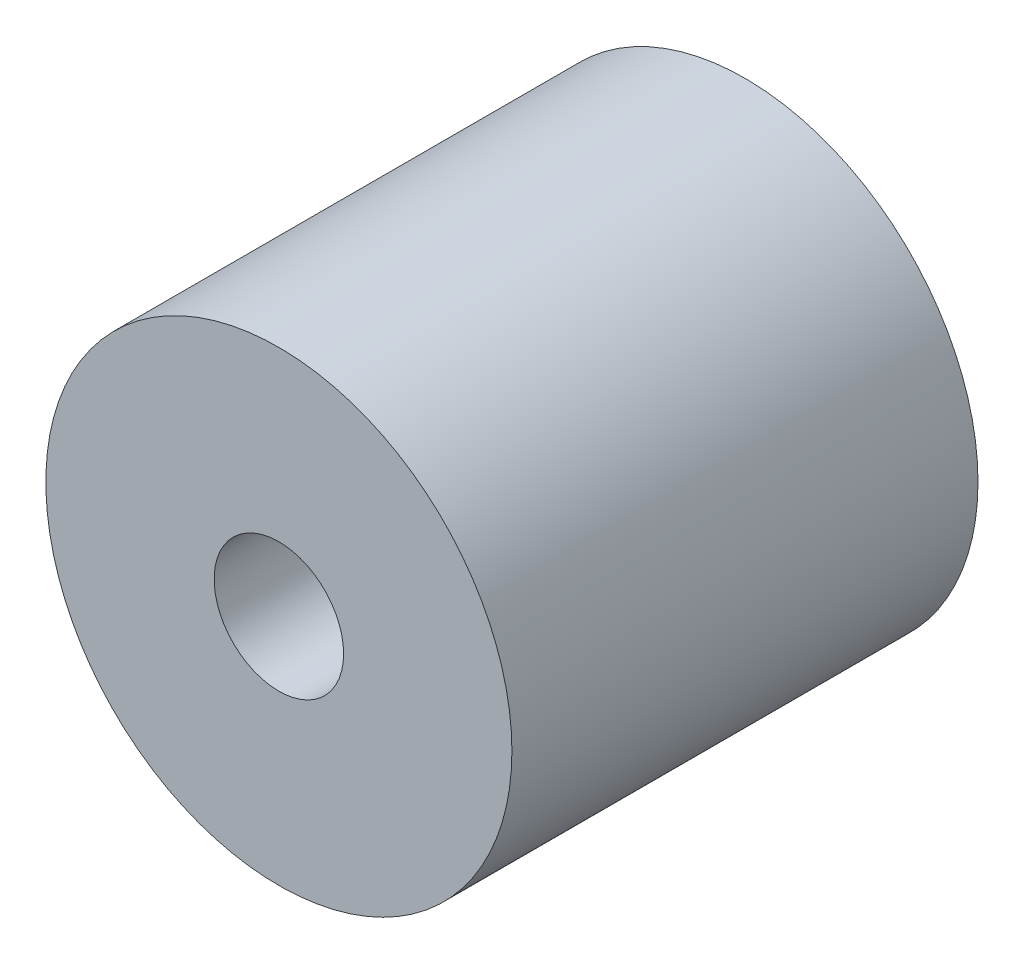
SolidWorks part; units mm, degrees
ref_plane "前视基准面" through (0, 0, 0) normal (0, 0, 1) x (1, 0, 0)
ref_plane "上视基准面" through (0, 0, 0) normal (0, 1, 0) x (1, 0, 0)
ref_plane "右视基准面" through (0, 0, 0) normal (1, 0, 0) x (0, 0, -1)
sketch "草图1" plane through (0, 0, 0) normal (0, 0, 1) x (1, 0, 0)
  circle A0 centre (0.7361, 4.9994) radius 9
  circle A1 centre (0.7361, 4.9994) radius 2.5
  dimension "D1" = 18
  dimension "D2" = 5
extrude "凸台-拉伸1" add sketch "草图1" along normal blind 18
sketch "草图2" plane through (0, 0, 18) normal (0, 0, 1) x (1, 0, 0)
